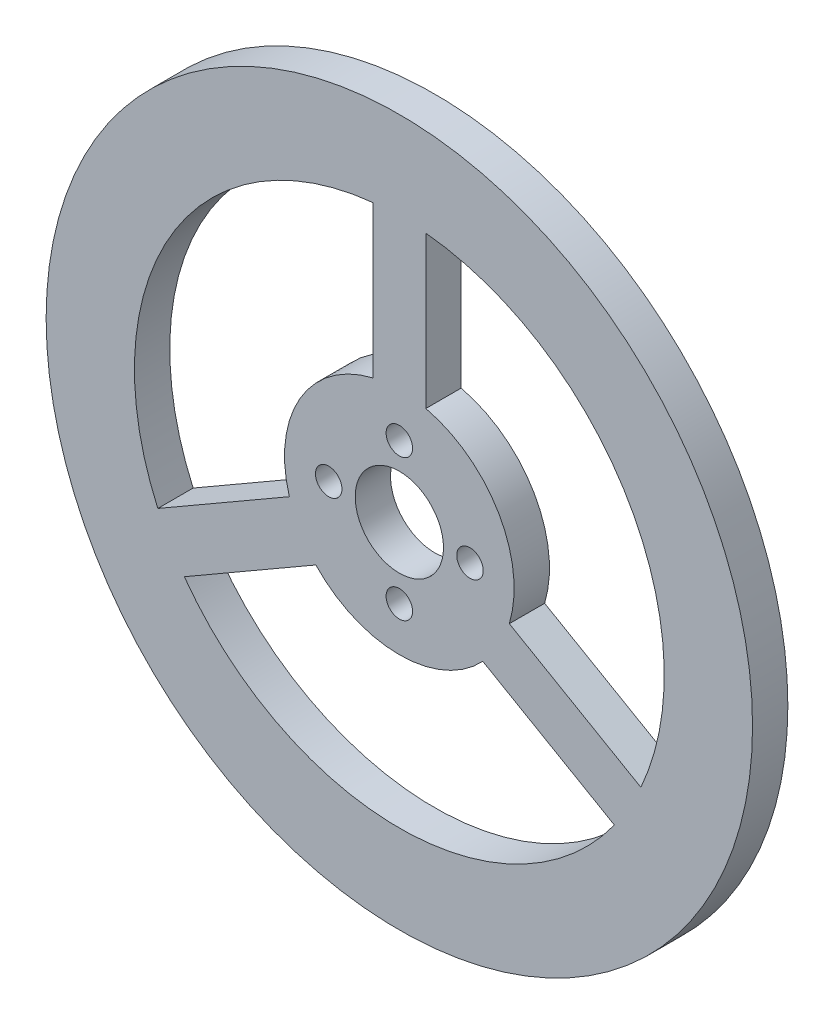
SolidWorks part; units mm, degrees
ref_plane "前视基准面" through (0, 0, 0) normal (0, 0, 1) x (1, 0, 0)
ref_plane "上视基准面" through (0, 0, 0) normal (0, 1, 0) x (1, 0, 0)
ref_plane "右视基准面" through (0, 0, 0) normal (1, 0, 0) x (0, 0, -1)
sketch "草图1" plane through (0, 0, 0) normal (0, 0, 1) x (1, 0, 0)
  circle A0 centre (0, 0) radius 40
  dimension "D1" = 80
extrude "凸台-拉伸1" add sketch "草图1" along normal blind 4
sketch "草图2" plane through (0, 0, 4) normal (0, 0, 1) x (1, 0, 0)
  line L0 (0, 0) -> (0, 73.1545) construction
  line L1 (0, 0) -> (63.3536, -36.5772) construction
  line L8 (0, 0) -> (-63.3536, -36.5772) construction
  line L9 (-3, 29.8496) -> (-3, 12.6491)
  line L10 (3, 29.8496) -> (3, 12.6491)
  line L11 (24.3505, -17.5229) -> (9.4545, -8.9226)
  line L12 (27.3505, -12.3267) -> (12.4545, -3.7265)
  line L13 (-27.3505, -12.3267) -> (-12.4545, -3.7265)
  line L14 (-24.3505, -17.5229) -> (-9.4545, -8.9226)
  circle A0 centre (0, 0) radius 5
  circle A2 centre (-8, 0) radius 1.5
  circle A3 centre (0, 8) radius 1.5
  circle A4 centre (8, 0) radius 1.5
  circle A5 centre (0, -8) radius 1.5
  arc A15 (-24.3505, -17.5229) -> (24.3505, -17.5229) centre (0, 0) ccw
  arc A16 (-3, 12.6491) -> (-12.4545, -3.7265) centre (0, 0) ccw
  arc A17 (-9.4545, -8.9226) -> (9.4545, -8.9226) centre (0, 0) ccw
  arc A18 (12.4545, -3.7265) -> (3, 12.6491) centre (0, 0) ccw
  arc A19 (27.3505, -12.3267) -> (3, 29.8496) centre (0, 0) ccw
  arc A20 (-3, 29.8496) -> (-27.3505, -12.3267) centre (0, 0) ccw
  point P14 (0, 0)
  point P19 (0, 0)
  point P21 (0, 0)
  point P33 (0, 0)
  dimension "D1" = 10
  dimension "D2" = 60
  dimension "D3" = 3
  dimension "D5" = 26
  dimension "D6" = 3
  dimension "D7" = 6
  dimension "D4" = 4
  dimension "D8" = 3
extrude "切除-拉伸1" cut sketch "草图2" against normal through all
